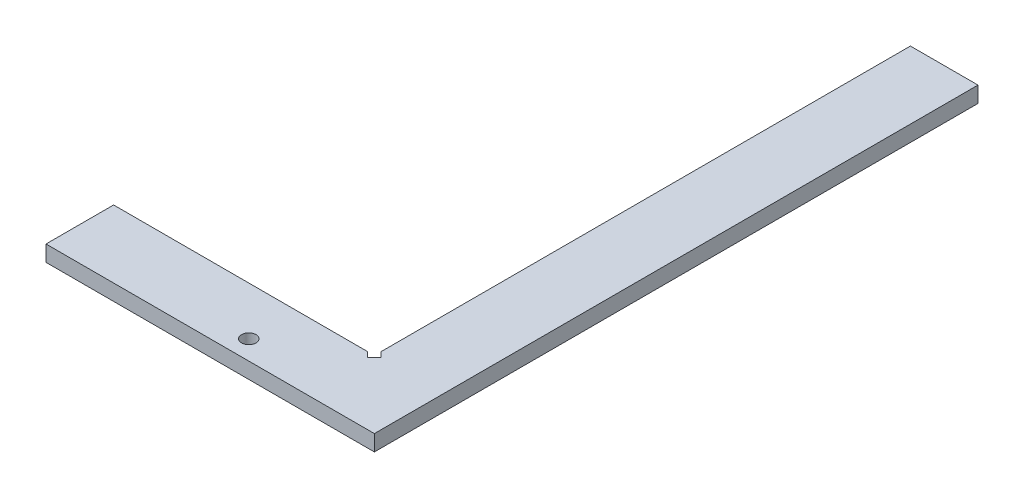
SolidWorks part; units mm, degrees
ref_plane "Спереди" through (0, 0, 0) normal (0, 0, 1) x (1, 0, 0)
ref_plane "Сверху" through (0, 0, 0) normal (0, 1, 0) x (1, 0, 0)
ref_plane "Справа" through (0, 0, 0) normal (1, 0, 0) x (0, 0, -1)
sketch "Эскиз1" plane through (0, 0, 0) normal (0, 1, 0) x (1, 0, 0)
  line L0 (0, 0) -> (0, 125)
  line L1 (0, 125) -> (-14, 125)
  line L2 (-14, 125) -> (-14, 14)
  line L3 (-14, 14) -> (-68, 14)
  line L4 (-68, 14) -> (-68, 0)
  line L5 (-68, 0) -> (0, 0)
  circle A0 centre (-30, 4) radius 1.5
  point P9 (0, 0)
extrude "Бобышка-Вытянуть1" add sketch "Эскиз1" along normal blind 3.3
sketch "Эскиз2" plane through (0, 3.3, 0) normal (0, 1, 0) x (1, 0, 0)
  line L0 (-15.4, 14) -> (-14.3393, 12.9393)
  line L1 (-14, 14) -> (-68, 14) construction
  line L2 (-14.3393, 12.9393) -> (-12.9393, 14.3393)
  line L3 (-12.9393, 14.3393) -> (-14, 15.4)
  line L4 (-14, 125) -> (-14, 14) construction
  line L5 (-15.4, 14) -> (-14, 15.4)
  point P4 (0, 0)
  point P10 (0, 0)
extrude "Вырез-Вытянуть1" cut sketch "Эскиз2" against normal blind 3.3
